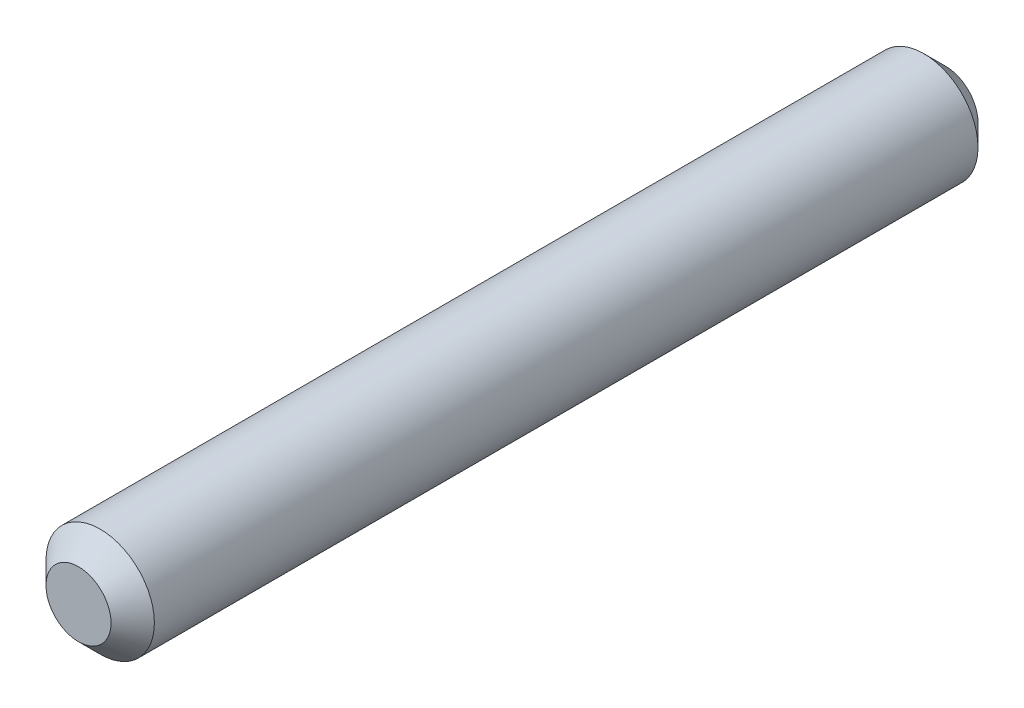
SolidWorks part; units mm, degrees
ref_plane "Спереди" through (0, 0, 0) normal (0, 0, 1) x (1, 0, 0)
ref_plane "Сверху" through (0, 0, 0) normal (0, 1, 0) x (1, 0, 0)
ref_plane "Справа" through (0, 0, 0) normal (1, 0, 0) x (0, 0, -1)
sketch "Эскиз1" plane through (0, 0, 0) normal (0, 0, 1) x (1, 0, 0)
  circle A0 centre (0, 0) radius 2.5
  dimension "D1" = 5
extrude "Бобышка-Вытянуть1" add sketch "Эскиз1" along normal blind 40
chamfer "Фаска1" distance 1 angle 45 1 edges at (2.5, 0, 40)
chamfer "Фаска2" distance 1 angle 45 1 edges at (2.5, 0, 0)
sketch "Эскиз2" plane through (0, 0, 0) normal (0, 1, 0) x (1, 0, 0)
  line L0 (2.5, -39) -> (-2.5, -39) construction
  line L1 (2.5, -39) -> (-2.5, -39) construction
  line L2 (0, -39) -> (0, -1) construction
  line L3 (2.5, -1) -> (-2.5, -1) construction
  line L4 (2.5, -1) -> (-2.5, -1) construction
  line L5 (0, -37) -> (-2.5, -37) construction
  line L6 (-2.5, -39) -> (-2.5, -37) construction
  line L7 (0, -3) -> (-2.5, -3) construction
  line L8 (-2.5, -1) -> (-2.5, -3) construction
  line L10 (0, -20) -> (-2.5, -20) construction
  line L11 (-2.5, -37) -> (-2.5, -20) construction
  dimension "D1" = 2
  dimension "D2" = 2
ref_plane "Г" through (0, 0, 37) normal (0, 0, -1) x (-1, 0, 0)
ref_plane "Г2" through (0, 0, 3) normal (0, 0, -1) x (-1, 0, 0)
ref_plane "V" through (0, 0, 20) normal (0, 0, -1) x (-1, 0, 0)
